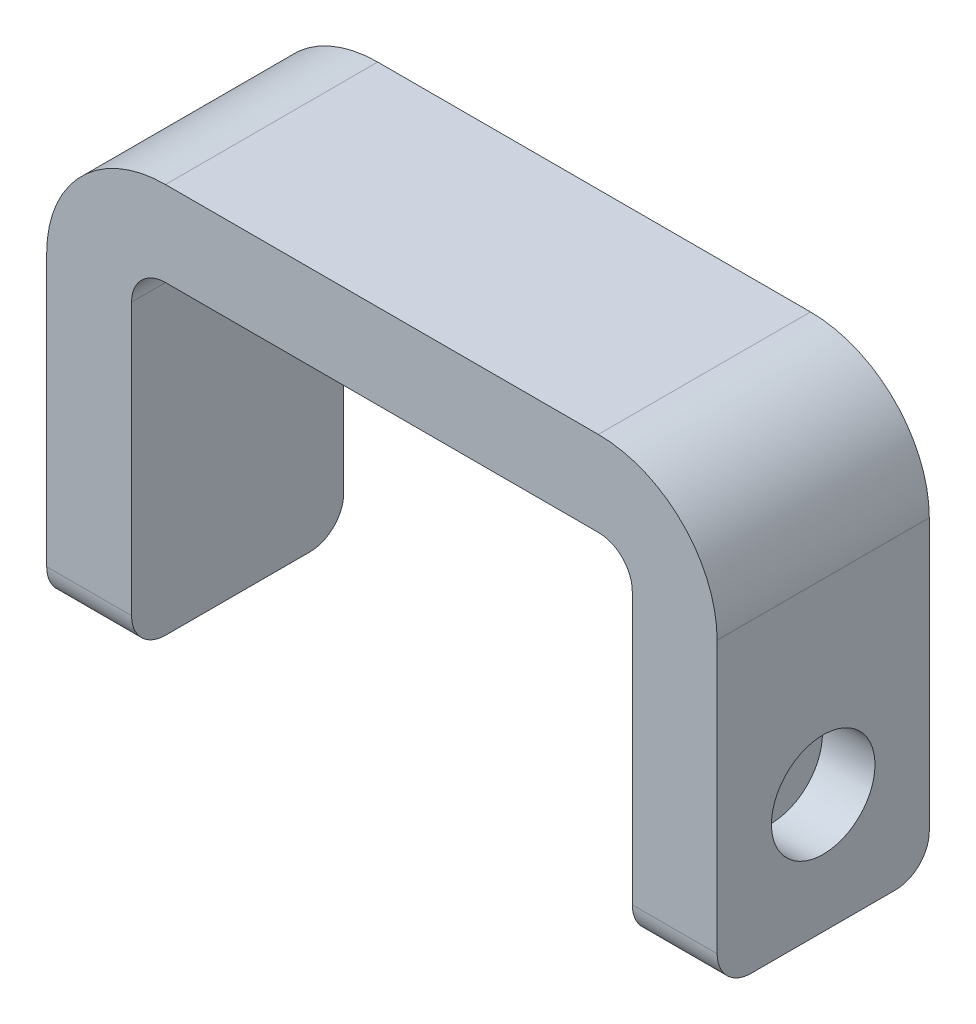
SolidWorks part; units mm, degrees
ref_plane "Front Plane" through (0, 0, 0) normal (0, 0, 1) x (1, 0, 0)
ref_plane "Top Plane" through (0, 0, 0) normal (0, 1, 0) x (1, 0, 0)
ref_plane "Right Plane" through (0, 0, 0) normal (1, 0, 0) x (0, 0, -1)
sketch "Sketch1" plane through (0, 0, 0) normal (0, 0, 1) x (1, 0, 0)
  line L0 (-14.75, 0) -> (-19.75, 0)
  line L1 (-19.75, 0) -> (-19.75, 25)
  line L2 (-19.75, 25) -> (19.75, 25)
  line L3 (-14.75, 0) -> (-14.75, 20)
  line L4 (-14.75, 20) -> (14.75, 20)
  line L5 (0, 0) -> (0, 11.8807) construction
  line L6 (14.75, 0) -> (14.75, 20)
  line L7 (19.75, 0) -> (19.75, 25)
  line L8 (14.75, 0) -> (19.75, 0)
  point P12 (0, 20)
  point P14 (0, 25)
  dimension "D1" = 29.5
  dimension "D2" = 5
  dimension "D3" = 5
  dimension "D4" = 20
extrude "Boss-Extrude1" add sketch "Sketch1" along normal mid plane 12.5
sketch "Sketch2" plane through (-19.75, 0, 0) normal (-1, 0, 0) x (0, 0, 1)
  line L0 (0, 0) -> (0, 25) construction
  line L1 (6.25, 0) -> (-6.25, 0) construction
  line L2 (6.25, 25) -> (-6.25, 25) construction
  circle A0 centre (0, 7) radius 3.05
  dimension "D1" = 6.1
  dimension "D2" = 7
extrude "Cut-Extrude1" cut sketch "Sketch2" against normal blind 3.1
mirror "Mirror1" about plane through (0, 0, 0) normal (1, 0, 0) of "Cut-Extrude1"
fillet "Fillet1" radius 2 2 edges at (14.75, 20, 0) (-14.75, 20, 0)
fillet "Fillet2" radius 7 2 edges at (19.75, 25, 0) (-19.75, 25, 0)
fillet "Fillet3" radius 2 4 edges at (17.25, 0, -6.25) (17.25, 0, 6.25) (-17.25, 0, -6.25) (-17.25, 0, 6.25)
equation "\"D3@Sketch1\"=\"D2@Sketch1\""
